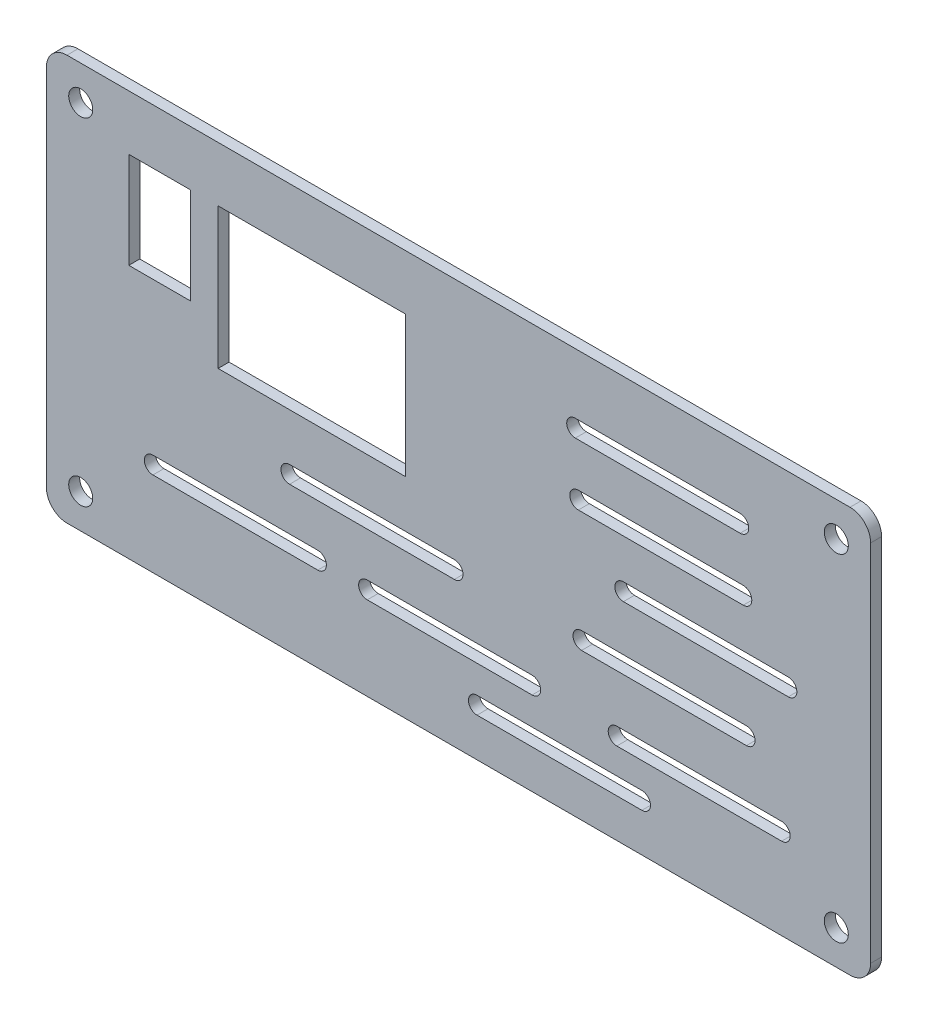
SolidWorks part; units mm, degrees
ref_plane "前视基准面" through (0, 0, 0) normal (0, 0, 1) x (1, 0, 0)
ref_plane "上视基准面" through (0, 0, 0) normal (0, 1, 0) x (1, 0, 0)
ref_plane "右视基准面" through (0, 0, 0) normal (1, 0, 0) x (0, 0, -1)
sketch "草图2" plane through (0, 0, 0) normal (0, 0, 1) x (1, 0, 0)
  line L0 (194.6195, 155.4932) -> (194.6195, 85.786) construction
  line L1 (137.6195, 153.3622) -> (251.6195, 153.3622)
  line L2 (134.6195, 150.3622) -> (134.6195, 97.3622)
  line L3 (137.6195, 94.3622) -> (251.6195, 94.3622)
  line L4 (254.6195, 150.3622) -> (254.6195, 97.3622)
  line L5 (134.6195, 153.3622) -> (254.6195, 94.3622) construction
  line L6 (134.6195, 94.3622) -> (254.6195, 153.3622) construction
  line L7 (138.0386, 123.8622) -> (280.1688, 123.8622) construction
  line L8 (211.6241, 143.3381) -> (235.6241, 143.3381) construction
  line L9 (159.6195, 145.3622) -> (186.9195, 145.3622)
  line L10 (159.6195, 145.3622) -> (159.6195, 124.8622)
  line L11 (159.6195, 124.8622) -> (186.9195, 124.8622)
  line L12 (186.9195, 145.3622) -> (186.9195, 124.8622)
  line L13 (159.6195, 145.3622) -> (186.9195, 124.8622) construction
  line L14 (159.6195, 124.8622) -> (186.9195, 145.3622) construction
  line L15 (211.6241, 144.5881) -> (235.6241, 144.5881)
  line L16 (211.6241, 142.0881) -> (235.6241, 142.0881)
  line L17 (212.0679, 134.4899) -> (236.0679, 134.4899) construction
  line L18 (212.0679, 135.7399) -> (236.0679, 135.7399)
  line L19 (212.0679, 133.2399) -> (236.0679, 133.2399)
  line L20 (218.6281, 126.2135) -> (242.6281, 126.2135) construction
  line L23 (212.5368, 117.0187) -> (236.5368, 117.0187) construction
  line L26 (212.5368, 118.2687) -> (236.5368, 118.2687)
  line L27 (212.5368, 115.7687) -> (236.5368, 115.7687)
  line L28 (217.6635, 107.5321) -> (241.6635, 107.5321) construction
  line L31 (150.1291, 107.9414) -> (174.1291, 107.9414) construction
  line L32 (150.1291, 109.1914) -> (174.1291, 109.1914)
  line L33 (150.1291, 106.6914) -> (174.1291, 106.6914)
  line L34 (181.3309, 107.7964) -> (205.3309, 107.7964) construction
  line L35 (181.3309, 109.0464) -> (205.3309, 109.0464)
  line L36 (181.3309, 106.5464) -> (205.3309, 106.5464)
  line L37 (217.6635, 108.7821) -> (241.6635, 108.7821)
  line L38 (217.6635, 106.2821) -> (241.6635, 106.2821)
  line L39 (218.6281, 127.4635) -> (242.6281, 127.4635)
  line L40 (218.6281, 124.9635) -> (242.6281, 124.9635)
  line L41 (170.0187, 116.7107) -> (194.0187, 116.7107) construction
  line L42 (170.0187, 117.9607) -> (194.0187, 117.9607)
  line L43 (170.0187, 115.4607) -> (194.0187, 115.4607)
  line L44 (197.3165, 101.2512) -> (221.3165, 101.2512) construction
  line L45 (197.3165, 102.5012) -> (221.3165, 102.5012)
  line L46 (197.3165, 100.0012) -> (221.3165, 100.0012)
  line L48 (146.6195, 145.3622) -> (155.6195, 145.3622)
  line L49 (146.6195, 145.3622) -> (146.6195, 131.3622)
  line L50 (146.6195, 131.3622) -> (155.6195, 131.3622)
  line L51 (155.6195, 145.3622) -> (155.6195, 131.3622)
  line L52 (146.6195, 145.3622) -> (155.6195, 131.3622) construction
  line L53 (146.6195, 131.3622) -> (155.6195, 145.3622) construction
  arc A0 (134.6195, 97.3622) -> (137.6195, 94.3622) centre (137.6195, 97.3622) ccw
  arc A1 (251.6195, 94.3622) -> (254.6195, 97.3622) centre (251.6195, 97.3622) ccw
  arc A2 (251.6195, 153.3622) -> (254.6195, 150.3622) centre (251.6195, 150.3622) cw
  arc A3 (137.6195, 153.3622) -> (134.6195, 150.3622) centre (137.6195, 150.3622) ccw
  circle A4 centre (139.6195, 99.3622) radius 1.75
  circle A5 centre (249.6195, 99.3622) radius 1.75
  circle A6 centre (249.6195, 148.3622) radius 1.75
  circle A7 centre (139.6195, 148.3622) radius 1.75
  arc A8 (211.6241, 144.5881) -> (211.6241, 142.0881) centre (211.6241, 143.3381) ccw
  arc A9 (235.6241, 142.0881) -> (235.6241, 144.5881) centre (235.6241, 143.3381) ccw
  arc A10 (212.0679, 135.7399) -> (212.0679, 133.2399) centre (212.0679, 134.4899) ccw
  arc A11 (236.0679, 133.2399) -> (236.0679, 135.7399) centre (236.0679, 134.4899) ccw
  arc A16 (212.5368, 118.2687) -> (212.5368, 115.7687) centre (212.5368, 117.0187) ccw
  arc A17 (236.5368, 115.7687) -> (236.5368, 118.2687) centre (236.5368, 117.0187) ccw
  arc A20 (150.1291, 109.1914) -> (150.1291, 106.6914) centre (150.1291, 107.9414) ccw
  arc A21 (174.1291, 106.6914) -> (174.1291, 109.1914) centre (174.1291, 107.9414) ccw
  arc A22 (181.3309, 109.0464) -> (181.3309, 106.5464) centre (181.3309, 107.7964) ccw
  arc A23 (205.3309, 106.5464) -> (205.3309, 109.0464) centre (205.3309, 107.7964) ccw
  arc A24 (217.6635, 108.7821) -> (217.6635, 106.2821) centre (217.6635, 107.5321) ccw
  arc A25 (241.6635, 106.2821) -> (241.6635, 108.7821) centre (241.6635, 107.5321) ccw
  arc A26 (218.6281, 127.4635) -> (218.6281, 124.9635) centre (218.6281, 126.2135) ccw
  arc A27 (242.6281, 124.9635) -> (242.6281, 127.4635) centre (242.6281, 126.2135) ccw
  arc A28 (170.0187, 117.9607) -> (170.0187, 115.4607) centre (170.0187, 116.7107) ccw
  arc A29 (194.0187, 115.4607) -> (194.0187, 117.9607) centre (194.0187, 116.7107) ccw
  arc A30 (197.3165, 102.5012) -> (197.3165, 100.0012) centre (197.3165, 101.2512) ccw
  arc A31 (221.3165, 100.0012) -> (221.3165, 102.5012) centre (221.3165, 101.2512) ccw
  point P0 (194.6195, 123.8622)
  point P29 (173.2695, 135.1122)
  point P36 (223.6241, 143.3381)
  point P43 (224.0679, 134.4899)
  point P50 (230.6281, 126.2135)
  point P57 (224.5368, 117.0187)
  point P62 (151.1195, 138.3622)
  point P72 (229.6635, 107.5321)
  point P79 (162.1291, 107.9414)
  point P86 (193.3309, 107.7964)
  point P93 (182.0187, 116.7107)
  point P100 (209.3165, 101.2512)
  dimension "D3" = 3
  dimension "D4" = 3.5
  dimension "D5" = 5
  dimension "D6" = 5
  dimension "D1" = 120
  dimension "D2" = 59
  dimension "D7" = 27.3
  dimension "D8" = 20.5
  dimension "D9" = 8
  dimension "D10" = 25
  dimension "D11" = 24
  dimension "D12" = 2.5
  dimension "D13" = 14
  dimension "D14" = 9
  dimension "D15" = 4
extrude "凸台-拉伸1" add sketch "草图2" along normal blind 1.6
